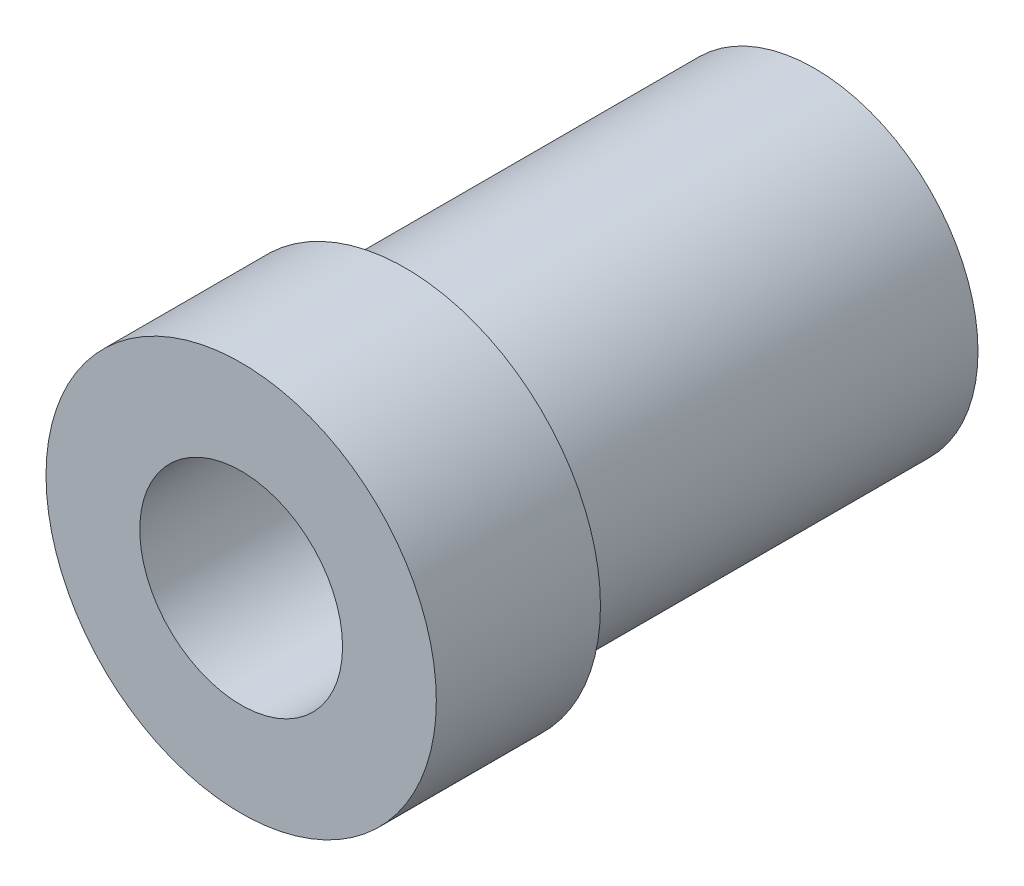
SolidWorks part; units mm, degrees
ref_plane "Front Plane" through (0, 0, 0) normal (0, 0, 1) x (1, 0, 0)
ref_plane "Top Plane" through (0, 0, 0) normal (0, 1, 0) x (1, 0, 0)
ref_plane "Right Plane" through (0, 0, 0) normal (1, 0, 0) x (0, 0, -1)
sketch "Sketch1" plane through (0, 0, 0) normal (1, 0, 0) x (0, 0, -1)
  line L0 (0, 0) -> (10.1421, 0) construction
  line L1 (10.0256, 2.4815) -> (10.0256, 3.9997)
  line L2 (10.0256, 3.9997) -> (0.0101, 3.9997)
  line L3 (0.0101, 3.9997) -> (0.0101, 4.776)
  line L4 (0.0101, 4.776) -> (-4.007, 4.776)
  line L5 (-4.007, 4.776) -> (-4.007, 2.4815)
  line L6 (-4.007, 2.4815) -> (10.0256, 2.4815)
revolve "Revolve1" add sketch "Sketch1" angle 360 about L0
